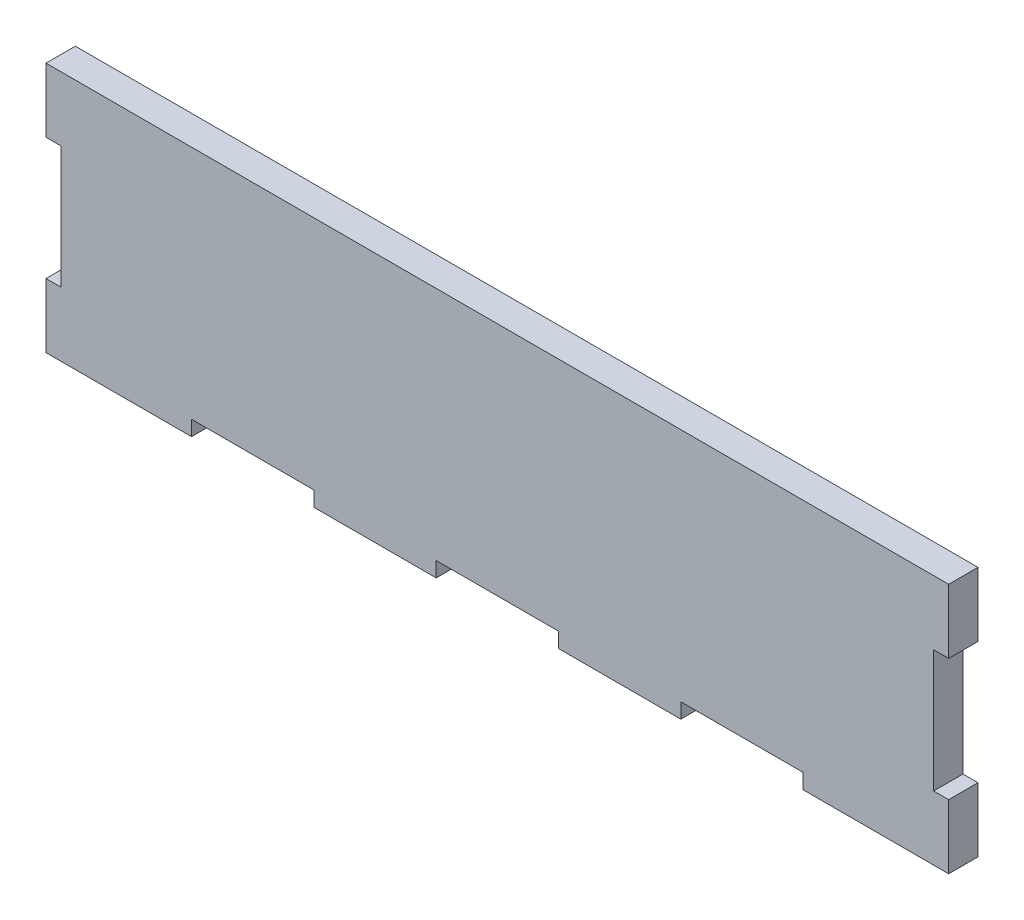
SolidWorks part; units mm, degrees
ref_plane "Alzado" through (0, 0, 0) normal (0, 0, 1) x (1, 0, 0)
ref_plane "Planta" through (0, 0, 0) normal (0, 1, 0) x (1, 0, 0)
ref_plane "Vista lateral" through (0, 0, 0) normal (1, 0, 0) x (0, 0, -1)
sketch "Model" plane through (0, 0, 0) normal (0, 0, 1) x (1, 0, 0)
  line L0 (0, 103) -> (0, 90.195)
  line L1 (0, 90.195) -> (3, 90.195)
  line L2 (3, 90.195) -> (3, 65.805)
  line L3 (3, 65.805) -> (0, 65.805)
  line L4 (0, 65.805) -> (0, 53)
  line L5 (0, 53) -> (29.025, 53)
  line L6 (29.025, 53) -> (29.025, 56)
  line L7 (29.025, 56) -> (53.415, 56)
  line L8 (53.415, 56) -> (53.415, 53)
  line L9 (53.415, 53) -> (77.805, 53)
  line L10 (77.805, 53) -> (77.805, 56)
  line L11 (77.805, 56) -> (102.195, 56)
  line L12 (102.195, 56) -> (102.195, 53)
  line L13 (102.195, 53) -> (126.585, 53)
  line L14 (126.585, 53) -> (126.585, 56)
  line L15 (126.585, 56) -> (150.975, 56)
  line L16 (150.975, 56) -> (150.975, 53)
  line L17 (150.975, 53) -> (175.365, 53)
  line L18 (175.365, 53) -> (180, 53)
  line L19 (180, 53) -> (180, 65.805)
  line L20 (180, 65.805) -> (177, 65.805)
  line L21 (177, 65.805) -> (177, 90.195)
  line L22 (177, 90.195) -> (180, 90.195)
  line L23 (180, 90.195) -> (180, 103)
  line L24 (180, 103) -> (0, 103)
extrude "Saliente-Extruir1" add sketch "Model" along normal blind 5.85
